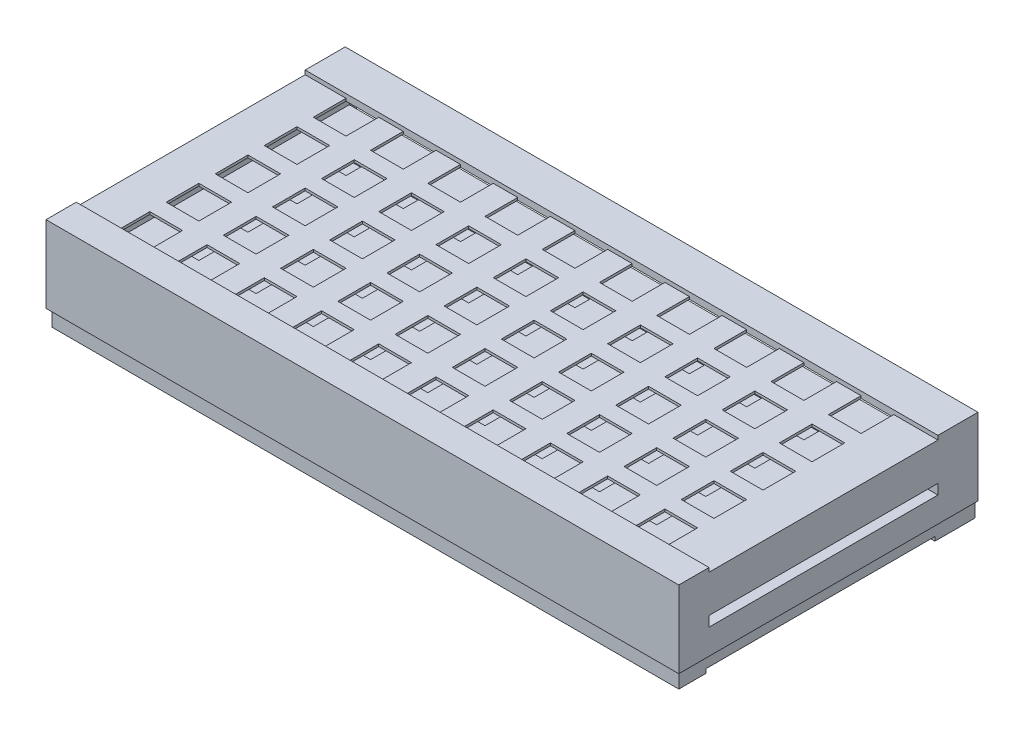
SolidWorks part; units mm, degrees
material "ABS"
ref_plane "Płaszczyzna przednia" through (0, 0, 0) normal (0, 0, 1) x (1, 0, 0)
ref_plane "Płaszczyzna górna" through (0, 0, 0) normal (0, 1, 0) x (1, 0, 0)
ref_plane "Płaszczyzna prawa" through (0, 0, 0) normal (1, 0, 0) x (0, 0, -1)
sketch "Szkic1" plane through (0, 0, 0) normal (0, 0, 1) x (1, 0, 0)
  line L15 (186, 34.1) -> (-188, 34.1)
  line L16 (186, 34.1) -> (186, -18.9)
  line L17 (186, -18.9) -> (-188, -18.9)
  line L18 (-188, 34.1) -> (-188, -18.9)
  point P0 (0, 0)
  dimension "D3" = 374
  dimension "D6" = 53
extrude "Dodanie-wyciągnięcie1" add sketch "Szkic1" along normal blind 177 contours L17 L18 L15 L16
sketch "Szkic5" plane through (0, -18.9, 0) normal (0, -1, 0) x (1, 0, 0)
  line L0 (186, 0) -> (-188, 0) construction
  line L1 (165.5, 48.5) -> (145.5, 48.5)
  line L2 (186, 177) -> (186, 0) construction
  line L3 (165.5, 48.5) -> (165.5, 68.5)
  line L4 (165.5, 68.5) -> (145.5, 68.5)
  line L5 (165.5, 18.5) -> (145.5, 18.5)
  line L6 (165.5, 18.5) -> (165.5, 38.5)
  line L7 (165.5, 38.5) -> (145.5, 38.5)
  line L8 (145.5, 18.5) -> (145.5, 38.5)
  line L9 (145.5, 48.5) -> (145.5, 68.5)
  line L10 (165.5, 78.5) -> (145.5, 78.5)
  line L11 (165.5, 78.5) -> (165.5, 98.5)
  line L12 (165.5, 98.5) -> (145.5, 98.5)
  line L13 (145.5, 78.5) -> (145.5, 98.5)
  line L14 (165.5, 108.5) -> (145.5, 108.5)
  line L15 (165.5, 108.5) -> (165.5, 128.5)
  line L16 (165.5, 128.5) -> (145.5, 128.5)
  line L17 (145.5, 108.5) -> (145.5, 128.5)
  line L18 (165.5, 138.5) -> (145.5, 138.5)
  line L19 (165.5, 138.5) -> (165.5, 158.5)
  line L20 (165.5, 158.5) -> (145.5, 158.5)
  line L21 (145.5, 138.5) -> (145.5, 158.5)
  line L22 (130.5, 48.5) -> (110.5, 48.5)
  line L23 (130.5, 48.5) -> (130.5, 68.5)
  line L24 (130.5, 68.5) -> (110.5, 68.5)
  line L25 (130.5, 18.5) -> (110.5, 18.5)
  line L26 (130.5, 18.5) -> (130.5, 38.5)
  line L27 (130.5, 38.5) -> (110.5, 38.5)
  line L28 (110.5, 18.5) -> (110.5, 38.5)
  line L29 (110.5, 48.5) -> (110.5, 68.5)
  line L30 (130.5, 78.5) -> (110.5, 78.5)
  line L31 (130.5, 78.5) -> (130.5, 98.5)
  line L32 (130.5, 98.5) -> (110.5, 98.5)
  line L33 (110.5, 78.5) -> (110.5, 98.5)
  line L34 (130.5, 108.5) -> (110.5, 108.5)
  line L35 (130.5, 108.5) -> (130.5, 128.5)
  line L36 (130.5, 128.5) -> (110.5, 128.5)
  line L37 (110.5, 108.5) -> (110.5, 128.5)
  line L38 (130.5, 138.5) -> (110.5, 138.5)
  line L39 (130.5, 138.5) -> (130.5, 158.5)
  line L40 (130.5, 158.5) -> (110.5, 158.5)
  line L41 (110.5, 138.5) -> (110.5, 158.5)
  line L42 (95.5, 48.5) -> (75.5, 48.5)
  line L43 (95.5, 48.5) -> (95.5, 68.5)
  line L44 (95.5, 68.5) -> (75.5, 68.5)
  line L45 (95.5, 18.5) -> (75.5, 18.5)
  line L46 (95.5, 18.5) -> (95.5, 38.5)
  line L47 (95.5, 38.5) -> (75.5, 38.5)
  line L48 (75.5, 18.5) -> (75.5, 38.5)
  line L49 (75.5, 48.5) -> (75.5, 68.5)
  line L50 (95.5, 78.5) -> (75.5, 78.5)
  line L51 (95.5, 78.5) -> (95.5, 98.5)
  line L52 (95.5, 98.5) -> (75.5, 98.5)
  line L53 (75.5, 78.5) -> (75.5, 98.5)
  line L54 (95.5, 108.5) -> (75.5, 108.5)
  line L55 (95.5, 108.5) -> (95.5, 128.5)
  line L56 (95.5, 128.5) -> (75.5, 128.5)
  line L57 (75.5, 108.5) -> (75.5, 128.5)
  line L58 (95.5, 138.5) -> (75.5, 138.5)
  line L59 (95.5, 138.5) -> (95.5, 158.5)
  line L60 (95.5, 158.5) -> (75.5, 158.5)
  line L61 (75.5, 138.5) -> (75.5, 158.5)
  line L62 (60.5, 48.5) -> (40.5, 48.5)
  line L63 (60.5, 48.5) -> (60.5, 68.5)
  line L64 (60.5, 68.5) -> (40.5, 68.5)
  line L65 (60.5, 18.5) -> (40.5, 18.5)
  line L66 (60.5, 18.5) -> (60.5, 38.5)
  line L67 (60.5, 38.5) -> (40.5, 38.5)
  line L68 (40.5, 18.5) -> (40.5, 38.5)
  line L69 (40.5, 48.5) -> (40.5, 68.5)
  line L70 (60.5, 78.5) -> (40.5, 78.5)
  line L71 (60.5, 78.5) -> (60.5, 98.5)
  line L72 (60.5, 98.5) -> (40.5, 98.5)
  line L73 (40.5, 78.5) -> (40.5, 98.5)
  line L74 (60.5, 108.5) -> (40.5, 108.5)
  line L75 (60.5, 108.5) -> (60.5, 128.5)
  line L76 (60.5, 128.5) -> (40.5, 128.5)
  line L77 (40.5, 108.5) -> (40.5, 128.5)
  line L78 (60.5, 138.5) -> (40.5, 138.5)
  line L79 (60.5, 138.5) -> (60.5, 158.5)
  line L80 (60.5, 158.5) -> (40.5, 158.5)
  line L81 (40.5, 138.5) -> (40.5, 158.5)
  line L82 (25.5, 48.5) -> (5.5, 48.5)
  line L83 (25.5, 48.5) -> (25.5, 68.5)
  line L84 (25.5, 68.5) -> (5.5, 68.5)
  line L85 (25.5, 18.5) -> (5.5, 18.5)
  line L86 (25.5, 18.5) -> (25.5, 38.5)
  line L87 (25.5, 38.5) -> (5.5, 38.5)
  line L88 (5.5, 18.5) -> (5.5, 38.5)
  line L89 (5.5, 48.5) -> (5.5, 68.5)
  line L90 (25.5, 78.5) -> (5.5, 78.5)
  line L91 (25.5, 78.5) -> (25.5, 98.5)
  line L92 (25.5, 98.5) -> (5.5, 98.5)
  line L93 (5.5, 78.5) -> (5.5, 98.5)
  line L94 (25.5, 108.5) -> (5.5, 108.5)
  line L95 (25.5, 108.5) -> (25.5, 128.5)
  line L96 (25.5, 128.5) -> (5.5, 128.5)
  line L97 (5.5, 108.5) -> (5.5, 128.5)
  line L98 (25.5, 138.5) -> (5.5, 138.5)
  line L99 (25.5, 138.5) -> (25.5, 158.5)
  line L100 (25.5, 158.5) -> (5.5, 158.5)
  line L101 (5.5, 138.5) -> (5.5, 158.5)
  line L102 (-9.5, 48.5) -> (-29.5, 48.5)
  line L103 (-9.5, 48.5) -> (-9.5, 68.5)
  line L104 (-9.5, 68.5) -> (-29.5, 68.5)
  line L105 (-9.5, 18.5) -> (-29.5, 18.5)
  line L106 (-9.5, 18.5) -> (-9.5, 38.5)
  line L107 (-9.5, 38.5) -> (-29.5, 38.5)
  line L108 (-29.5, 18.5) -> (-29.5, 38.5)
  line L109 (-29.5, 48.5) -> (-29.5, 68.5)
  line L110 (-9.5, 78.5) -> (-29.5, 78.5)
  line L111 (-9.5, 78.5) -> (-9.5, 98.5)
  line L112 (-9.5, 98.5) -> (-29.5, 98.5)
  line L113 (-29.5, 78.5) -> (-29.5, 98.5)
  line L114 (-9.5, 108.5) -> (-29.5, 108.5)
  line L115 (-9.5, 108.5) -> (-9.5, 128.5)
  line L116 (-9.5, 128.5) -> (-29.5, 128.5)
  line L117 (-29.5, 108.5) -> (-29.5, 128.5)
  line L118 (-9.5, 138.5) -> (-29.5, 138.5)
  line L119 (-9.5, 138.5) -> (-9.5, 158.5)
  line L120 (-9.5, 158.5) -> (-29.5, 158.5)
  line L121 (-29.5, 138.5) -> (-29.5, 158.5)
  line L122 (-44.5, 48.5) -> (-64.5, 48.5)
  line L123 (-44.5, 48.5) -> (-44.5, 68.5)
  line L124 (-44.5, 68.5) -> (-64.5, 68.5)
  line L125 (-44.5, 18.5) -> (-64.5, 18.5)
  line L126 (-44.5, 18.5) -> (-44.5, 38.5)
  line L127 (-44.5, 38.5) -> (-64.5, 38.5)
  line L128 (-64.5, 18.5) -> (-64.5, 38.5)
  line L129 (-64.5, 48.5) -> (-64.5, 68.5)
  line L130 (-44.5, 78.5) -> (-64.5, 78.5)
  line L131 (-44.5, 78.5) -> (-44.5, 98.5)
  line L132 (-44.5, 98.5) -> (-64.5, 98.5)
  line L133 (-64.5, 78.5) -> (-64.5, 98.5)
  line L134 (-44.5, 108.5) -> (-64.5, 108.5)
  line L135 (-44.5, 108.5) -> (-44.5, 128.5)
  line L136 (-44.5, 128.5) -> (-64.5, 128.5)
  line L137 (-64.5, 108.5) -> (-64.5, 128.5)
  line L138 (-44.5, 138.5) -> (-64.5, 138.5)
  line L139 (-44.5, 138.5) -> (-44.5, 158.5)
  line L140 (-44.5, 158.5) -> (-64.5, 158.5)
  line L141 (-64.5, 138.5) -> (-64.5, 158.5)
  line L142 (-79.5, 48.5) -> (-99.5, 48.5)
  line L143 (-79.5, 48.5) -> (-79.5, 68.5)
  line L144 (-79.5, 68.5) -> (-99.5, 68.5)
  line L145 (-79.5, 18.5) -> (-99.5, 18.5)
  line L146 (-79.5, 18.5) -> (-79.5, 38.5)
  line L147 (-79.5, 38.5) -> (-99.5, 38.5)
  line L148 (-99.5, 18.5) -> (-99.5, 38.5)
  line L149 (-99.5, 48.5) -> (-99.5, 68.5)
  line L150 (-79.5, 78.5) -> (-99.5, 78.5)
  line L151 (-79.5, 78.5) -> (-79.5, 98.5)
  line L152 (-79.5, 98.5) -> (-99.5, 98.5)
  line L153 (-99.5, 78.5) -> (-99.5, 98.5)
  line L154 (-79.5, 108.5) -> (-99.5, 108.5)
  line L155 (-79.5, 108.5) -> (-79.5, 128.5)
  line L156 (-79.5, 128.5) -> (-99.5, 128.5)
  line L157 (-99.5, 108.5) -> (-99.5, 128.5)
  line L158 (-79.5, 138.5) -> (-99.5, 138.5)
  line L159 (-79.5, 138.5) -> (-79.5, 158.5)
  line L160 (-79.5, 158.5) -> (-99.5, 158.5)
  line L161 (-99.5, 138.5) -> (-99.5, 158.5)
  line L162 (-114.5, 48.5) -> (-134.5, 48.5)
  line L163 (-114.5, 48.5) -> (-114.5, 68.5)
  line L164 (-114.5, 68.5) -> (-134.5, 68.5)
  line L165 (-114.5, 18.5) -> (-134.5, 18.5)
  line L166 (-114.5, 18.5) -> (-114.5, 38.5)
  line L167 (-114.5, 38.5) -> (-134.5, 38.5)
  line L168 (-134.5, 18.5) -> (-134.5, 38.5)
  line L169 (-134.5, 48.5) -> (-134.5, 68.5)
  line L170 (-114.5, 78.5) -> (-134.5, 78.5)
  line L171 (-114.5, 78.5) -> (-114.5, 98.5)
  line L172 (-114.5, 98.5) -> (-134.5, 98.5)
  line L173 (-134.5, 78.5) -> (-134.5, 98.5)
  line L174 (-114.5, 108.5) -> (-134.5, 108.5)
  line L175 (-114.5, 108.5) -> (-114.5, 128.5)
  line L176 (-114.5, 128.5) -> (-134.5, 128.5)
  line L177 (-134.5, 108.5) -> (-134.5, 128.5)
  line L178 (-114.5, 138.5) -> (-134.5, 138.5)
  line L179 (-114.5, 138.5) -> (-114.5, 158.5)
  line L180 (-114.5, 158.5) -> (-134.5, 158.5)
  line L181 (-134.5, 138.5) -> (-134.5, 158.5)
  line L182 (-149.5, 48.5) -> (-169.5, 48.5)
  line L183 (-149.5, 48.5) -> (-149.5, 68.5)
  line L184 (-149.5, 68.5) -> (-169.5, 68.5)
  line L185 (-149.5, 18.5) -> (-169.5, 18.5)
  line L186 (-149.5, 18.5) -> (-149.5, 38.5)
  line L187 (-149.5, 38.5) -> (-169.5, 38.5)
  line L188 (-169.5, 18.5) -> (-169.5, 38.5)
  line L189 (-169.5, 48.5) -> (-169.5, 68.5)
  line L190 (-149.5, 78.5) -> (-169.5, 78.5)
  line L191 (-149.5, 78.5) -> (-149.5, 98.5)
  line L192 (-149.5, 98.5) -> (-169.5, 98.5)
  line L193 (-169.5, 78.5) -> (-169.5, 98.5)
  line L194 (-149.5, 108.5) -> (-169.5, 108.5)
  line L195 (-149.5, 108.5) -> (-149.5, 128.5)
  line L196 (-149.5, 128.5) -> (-169.5, 128.5)
  line L197 (-169.5, 108.5) -> (-169.5, 128.5)
  line L198 (-149.5, 138.5) -> (-169.5, 138.5)
  line L199 (-149.5, 138.5) -> (-149.5, 158.5)
  line L200 (-149.5, 158.5) -> (-169.5, 158.5)
  line L201 (-169.5, 138.5) -> (-169.5, 158.5)
  line L202 (186, 177) -> (-188, 177) construction
  line L203 (-188, 177) -> (-188, 0) construction
  dimension "D1" = 18.5
  dimension "D2" = 20.5
  dimension "D3" = 20
  dimension "D4" = 20
  dimension "D7" = 20
  dimension "D8" = 20
  dimension "D9" = 15
  dimension "D10" = 18.5
  dimension "D11" = 18.5
  dimension "D5" = 5
  dimension "D6" = 10
extrude "Wytnij-wyciągnięcie4" cut sketch "Szkic5" against normal blind 104
sketch "Szkic7" plane through (0, 0, 0) normal (0, 0, -1) x (-1, 0, 0)
  line L5 (-186, -18.9) -> (188, -18.9) construction
  line L7 (-184, 32.1) -> (186, 32.1)
  line L8 (-184, 32.1) -> (-184, 12.7)
  line L9 (-184, 12.7) -> (186, 12.7)
  line L10 (186, 32.1) -> (186, 12.7)
  line L12 (-186, 34.1) -> (-186, -18.9) construction
  line L13 (-184, -16.9) -> (186, -16.9)
  line L14 (-184, -16.9) -> (-184, 2.5)
  line L15 (-184, 2.5) -> (186, 2.5)
  line L16 (186, -16.9) -> (186, 2.5)
  line L17 (-186, 34.1) -> (188, 34.1) construction
  dimension "D1" = 370
  dimension "D2" = 2
  dimension "D3" = 2
  dimension "D4" = 2
  dimension "D5" = 2
  dimension "D6" = 370
  dimension "D7" = 370
  dimension "D8" = 19.4
  dimension "D9" = 19.4
extrude "Wytnij-wyciągnięcie5" cut sketch "Szkic7" against normal blind 175
sketch "Szkic9" plane through (186, 0, 0) normal (1, 0, 0) x (0, 0, -1)
  line L15 (-158.5, 10.7) -> (-158.5, 4.5)
  line L17 (-18.5, 10.7) -> (-158.5, 10.7)
  line L18 (-18.5, 10.7) -> (-18.5, 4.5)
  line L19 (-18.5, 4.5) -> (-158.5, 4.5)
extrude "Wytnij-wyciągnięcie6" cut sketch "Szkic9" against normal blind 374
sketch "Szkic15" plane through (0, 34.1, 0) normal (0, 1, 0) x (1, 0, 0)
  line L1 (-188, 0) -> (186, 0)
  line L2 (-188, 0) -> (-188, -177)
  line L3 (-188, -177) -> (186, -177)
  line L4 (186, 0) -> (186, -177)
  line L5 (-169.5, -18.5) -> (-149.5, -18.5)
  line L6 (-169.5, -18.5) -> (-169.5, -38.5)
  line L7 (-169.5, -38.5) -> (-149.5, -38.5)
  line L8 (-149.5, -18.5) -> (-149.5, -38.5)
  line L9 (-134.5, -18.5) -> (-114.5, -18.5)
  line L10 (-134.5, -18.5) -> (-134.5, -38.5)
  line L11 (-134.5, -38.5) -> (-114.5, -38.5)
  line L12 (-114.5, -18.5) -> (-114.5, -38.5)
  line L13 (-99.5, -18.5) -> (-79.5, -18.5)
  line L14 (-99.5, -18.5) -> (-99.5, -38.5)
  line L15 (-99.5, -38.5) -> (-79.5, -38.5)
  line L16 (-79.5, -18.5) -> (-79.5, -38.5)
  line L17 (-64.5, -18.5) -> (-44.5, -18.5)
  line L18 (-64.5, -18.5) -> (-64.5, -38.5)
  line L19 (-64.5, -38.5) -> (-44.5, -38.5)
  line L20 (-44.5, -18.5) -> (-44.5, -38.5)
  line L21 (-29.5, -18.5) -> (-9.5, -18.5)
  line L22 (-29.5, -18.5) -> (-29.5, -38.5)
  line L23 (-29.5, -38.5) -> (-9.5, -38.5)
  line L24 (-9.5, -18.5) -> (-9.5, -38.5)
  line L25 (5.5, -18.5) -> (25.5, -18.5)
  line L26 (5.5, -18.5) -> (5.5, -38.5)
  line L27 (5.5, -38.5) -> (25.5, -38.5)
  line L28 (25.5, -18.5) -> (25.5, -38.5)
  line L29 (40.5, -18.5) -> (60.5, -18.5)
  line L30 (40.5, -18.5) -> (40.5, -38.5)
  line L31 (40.5, -38.5) -> (60.5, -38.5)
  line L32 (60.5, -18.5) -> (60.5, -38.5)
  line L33 (75.5, -18.5) -> (95.5, -18.5)
  line L34 (75.5, -18.5) -> (75.5, -38.5)
  line L35 (75.5, -38.5) -> (95.5, -38.5)
  line L36 (95.5, -18.5) -> (95.5, -38.5)
  line L37 (110.5, -18.5) -> (130.5, -18.5)
  line L38 (110.5, -18.5) -> (110.5, -38.5)
  line L39 (110.5, -38.5) -> (130.5, -38.5)
  line L40 (130.5, -18.5) -> (130.5, -38.5)
  line L41 (145.5, -18.5) -> (165.5, -18.5)
  line L42 (145.5, -18.5) -> (145.5, -38.5)
  line L43 (145.5, -38.5) -> (165.5, -38.5)
  line L44 (165.5, -18.5) -> (165.5, -38.5)
  line L45 (145.5, -48.5) -> (165.5, -48.5)
  line L46 (145.5, -48.5) -> (145.5, -68.5)
  line L47 (145.5, -68.5) -> (165.5, -68.5)
  line L48 (165.5, -48.5) -> (165.5, -68.5)
  line L49 (145.5, -78.5) -> (165.5, -78.5)
  line L50 (145.5, -78.5) -> (145.5, -98.5)
  line L51 (145.5, -98.5) -> (165.5, -98.5)
  line L52 (165.5, -78.5) -> (165.5, -98.5)
  line L53 (145.5, -108.5) -> (165.5, -108.5)
  line L54 (145.5, -108.5) -> (145.5, -128.5)
  line L55 (145.5, -128.5) -> (165.5, -128.5)
  line L56 (165.5, -108.5) -> (165.5, -128.5)
  line L57 (145.5, -138.5) -> (165.5, -138.5)
  line L58 (145.5, -138.5) -> (145.5, -158.5)
  line L59 (145.5, -158.5) -> (165.5, -158.5)
  line L60 (165.5, -138.5) -> (165.5, -158.5)
  line L61 (110.5, -48.5) -> (130.5, -48.5)
  line L62 (110.5, -48.5) -> (110.5, -68.5)
  line L63 (110.5, -68.5) -> (130.5, -68.5)
  line L64 (130.5, -48.5) -> (130.5, -68.5)
  line L65 (110.5, -78.5) -> (130.5, -78.5)
  line L66 (110.5, -78.5) -> (110.5, -98.5)
  line L67 (110.5, -98.5) -> (130.5, -98.5)
  line L68 (130.5, -78.5) -> (130.5, -98.5)
  line L69 (110.5, -108.5) -> (130.5, -108.5)
  line L70 (110.5, -108.5) -> (110.5, -128.5)
  line L71 (110.5, -128.5) -> (130.5, -128.5)
  line L72 (130.5, -108.5) -> (130.5, -128.5)
  line L73 (110.5, -138.5) -> (130.5, -138.5)
  line L74 (110.5, -138.5) -> (110.5, -158.5)
  line L75 (110.5, -158.5) -> (130.5, -158.5)
  line L76 (130.5, -138.5) -> (130.5, -158.5)
  line L77 (75.5, -48.5) -> (95.5, -48.5)
  line L78 (75.5, -48.5) -> (75.5, -68.5)
  line L79 (75.5, -68.5) -> (95.5, -68.5)
  line L80 (95.5, -48.5) -> (95.5, -68.5)
  line L81 (75.5, -78.5) -> (95.5, -78.5)
  line L82 (75.5, -78.5) -> (75.5, -98.5)
  line L83 (75.5, -98.5) -> (95.5, -98.5)
  line L84 (95.5, -78.5) -> (95.5, -98.5)
  line L85 (75.5, -108.5) -> (95.5, -108.5)
  line L86 (75.5, -108.5) -> (75.5, -128.5)
  line L87 (75.5, -128.5) -> (95.5, -128.5)
  line L88 (95.5, -108.5) -> (95.5, -128.5)
  line L89 (75.5, -138.5) -> (95.5, -138.5)
  line L90 (75.5, -138.5) -> (75.5, -158.5)
  line L91 (75.5, -158.5) -> (95.5, -158.5)
  line L92 (95.5, -138.5) -> (95.5, -158.5)
  line L93 (40.5, -48.5) -> (60.5, -48.5)
  line L94 (40.5, -48.5) -> (40.5, -68.5)
  line L95 (40.5, -68.5) -> (60.5, -68.5)
  line L96 (60.5, -48.5) -> (60.5, -68.5)
  line L97 (40.5, -78.5) -> (60.5, -78.5)
  line L98 (40.5, -78.5) -> (40.5, -98.5)
  line L99 (40.5, -98.5) -> (60.5, -98.5)
  line L100 (60.5, -78.5) -> (60.5, -98.5)
  line L101 (40.5, -108.5) -> (60.5, -108.5)
  line L102 (40.5, -108.5) -> (40.5, -128.5)
  line L103 (40.5, -128.5) -> (60.5, -128.5)
  line L104 (60.5, -108.5) -> (60.5, -128.5)
  line L105 (5.5, -48.5) -> (25.5, -48.5)
  line L106 (5.5, -48.5) -> (5.5, -68.5)
  line L107 (5.5, -68.5) -> (25.5, -68.5)
  line L108 (25.5, -48.5) -> (25.5, -68.5)
  line L109 (5.5, -78.5) -> (25.5, -78.5)
  line L110 (5.5, -78.5) -> (5.5, -98.5)
  line L111 (5.5, -98.5) -> (25.5, -98.5)
  line L112 (25.5, -78.5) -> (25.5, -98.5)
  line L113 (5.5, -108.5) -> (25.5, -108.5)
  line L114 (5.5, -108.5) -> (5.5, -128.5)
  line L115 (5.5, -128.5) -> (25.5, -128.5)
  line L116 (25.5, -108.5) -> (25.5, -128.5)
  line L117 (5.5, -138.5) -> (25.5, -138.5)
  line L118 (5.5, -138.5) -> (5.5, -158.5)
  line L119 (5.5, -158.5) -> (25.5, -158.5)
  line L120 (25.5, -138.5) -> (25.5, -158.5)
  line L121 (40.5, -138.5) -> (60.5, -138.5)
  line L122 (40.5, -138.5) -> (40.5, -158.5)
  line L123 (40.5, -158.5) -> (60.5, -158.5)
  line L124 (60.5, -138.5) -> (60.5, -158.5)
  line L125 (-29.5, -48.5) -> (-9.5, -48.5)
  line L126 (-29.5, -48.5) -> (-29.5, -68.5)
  line L127 (-29.5, -68.5) -> (-9.5, -68.5)
  line L128 (-9.5, -48.5) -> (-9.5, -68.5)
  line L129 (-29.5, -78.5) -> (-9.5, -78.5)
  line L130 (-29.5, -78.5) -> (-29.5, -98.5)
  line L131 (-29.5, -98.5) -> (-9.5, -98.5)
  line L132 (-9.5, -78.5) -> (-9.5, -98.5)
  line L133 (-29.5, -108.5) -> (-9.5, -108.5)
  line L134 (-29.5, -108.5) -> (-29.5, -128.5)
  line L135 (-29.5, -128.5) -> (-9.5, -128.5)
  line L136 (-9.5, -108.5) -> (-9.5, -128.5)
  line L137 (-29.5, -138.5) -> (-9.5, -138.5)
  line L138 (-29.5, -138.5) -> (-29.5, -158.5)
  line L139 (-29.5, -158.5) -> (-9.5, -158.5)
  line L140 (-9.5, -138.5) -> (-9.5, -158.5)
  line L141 (-64.5, -48.5) -> (-44.5, -48.5)
  line L142 (-64.5, -48.5) -> (-64.5, -68.5)
  line L143 (-64.5, -68.5) -> (-44.5, -68.5)
  line L144 (-44.5, -48.5) -> (-44.5, -68.5)
  line L145 (-64.5, -78.5) -> (-44.5, -78.5)
  line L146 (-64.5, -78.5) -> (-64.5, -98.5)
  line L147 (-64.5, -98.5) -> (-44.5, -98.5)
  line L148 (-44.5, -78.5) -> (-44.5, -98.5)
  line L149 (-64.5, -108.5) -> (-44.5, -108.5)
  line L150 (-64.5, -108.5) -> (-64.5, -128.5)
  line L151 (-64.5, -128.5) -> (-44.5, -128.5)
  line L152 (-44.5, -108.5) -> (-44.5, -128.5)
  line L153 (-64.5, -138.5) -> (-44.5, -138.5)
  line L154 (-64.5, -138.5) -> (-64.5, -158.5)
  line L155 (-64.5, -158.5) -> (-44.5, -158.5)
  line L156 (-44.5, -138.5) -> (-44.5, -158.5)
  line L157 (-99.5, -48.5) -> (-79.5, -48.5)
  line L158 (-99.5, -48.5) -> (-99.5, -68.5)
  line L159 (-99.5, -68.5) -> (-79.5, -68.5)
  line L160 (-79.5, -48.5) -> (-79.5, -68.5)
  line L161 (-99.5, -78.5) -> (-79.5, -78.5)
  line L162 (-99.5, -78.5) -> (-99.5, -98.5)
  line L163 (-99.5, -98.5) -> (-79.5, -98.5)
  line L164 (-79.5, -78.5) -> (-79.5, -98.5)
  line L165 (-99.5, -108.5) -> (-79.5, -108.5)
  line L166 (-99.5, -108.5) -> (-99.5, -128.5)
  line L167 (-99.5, -128.5) -> (-79.5, -128.5)
  line L168 (-79.5, -108.5) -> (-79.5, -128.5)
  line L169 (-99.5, -138.5) -> (-79.5, -138.5)
  line L170 (-99.5, -138.5) -> (-99.5, -158.5)
  line L171 (-99.5, -158.5) -> (-79.5, -158.5)
  line L172 (-79.5, -138.5) -> (-79.5, -158.5)
  line L173 (-134.5, -48.5) -> (-114.5, -48.5)
  line L174 (-134.5, -48.5) -> (-134.5, -68.5)
  line L175 (-134.5, -68.5) -> (-114.5, -68.5)
  line L176 (-114.5, -48.5) -> (-114.5, -68.5)
  line L177 (-134.5, -78.5) -> (-114.5, -78.5)
  line L178 (-134.5, -78.5) -> (-134.5, -98.5)
  line L179 (-134.5, -98.5) -> (-114.5, -98.5)
  line L180 (-114.5, -78.5) -> (-114.5, -98.5)
  line L181 (-134.5, -108.5) -> (-114.5, -108.5)
  line L182 (-134.5, -108.5) -> (-134.5, -128.5)
  line L183 (-134.5, -128.5) -> (-114.5, -128.5)
  line L184 (-114.5, -108.5) -> (-114.5, -128.5)
  line L185 (-134.5, -138.5) -> (-114.5, -138.5)
  line L186 (-134.5, -138.5) -> (-134.5, -158.5)
  line L187 (-134.5, -158.5) -> (-114.5, -158.5)
  line L188 (-114.5, -138.5) -> (-114.5, -158.5)
  line L189 (-169.5, -48.5) -> (-149.5, -48.5)
  line L190 (-169.5, -48.5) -> (-169.5, -68.5)
  line L191 (-169.5, -68.5) -> (-149.5, -68.5)
  line L192 (-149.5, -48.5) -> (-149.5, -68.5)
  line L193 (-169.5, -78.5) -> (-149.5, -78.5)
  line L194 (-169.5, -78.5) -> (-169.5, -98.5)
  line L195 (-169.5, -98.5) -> (-149.5, -98.5)
  line L196 (-149.5, -78.5) -> (-149.5, -98.5)
  line L197 (-169.5, -108.5) -> (-149.5, -108.5)
  line L198 (-169.5, -108.5) -> (-169.5, -128.5)
  line L199 (-169.5, -128.5) -> (-149.5, -128.5)
  line L200 (-149.5, -108.5) -> (-149.5, -128.5)
  line L201 (-169.5, -138.5) -> (-149.5, -138.5)
  line L202 (-169.5, -138.5) -> (-169.5, -158.5)
  line L203 (-169.5, -158.5) -> (-149.5, -158.5)
  line L204 (-149.5, -138.5) -> (-149.5, -158.5)
extrude "Dodanie-wyciągnięcie6" add sketch "Szkic15" along normal blind 1
sketch "Szkic16" plane through (0, -18.9, 0) normal (0, -1, 0) x (1, 0, 0)
  line L1 (186, 0) -> (-188, 0)
  line L2 (186, 0) -> (186, 177)
  line L3 (186, 177) -> (-188, 177)
  line L4 (-188, 0) -> (-188, 177)
  line L5 (165.5, 18.5) -> (145.5, 18.5)
  line L6 (165.5, 18.5) -> (165.5, 38.5)
  line L7 (165.5, 38.5) -> (145.5, 38.5)
  line L8 (145.5, 18.5) -> (145.5, 38.5)
  line L9 (130.5, 18.5) -> (110.5, 18.5)
  line L10 (130.5, 18.5) -> (130.5, 38.5)
  line L11 (130.5, 38.5) -> (110.5, 38.5)
  line L12 (110.5, 18.5) -> (110.5, 38.5)
  line L13 (95.5, 18.5) -> (75.5, 18.5)
  line L14 (95.5, 18.5) -> (95.5, 38.5)
  line L15 (95.5, 38.5) -> (75.5, 38.5)
  line L16 (75.5, 18.5) -> (75.5, 38.5)
  line L17 (60.5, 18.5) -> (40.5, 18.5)
  line L18 (60.5, 18.5) -> (60.5, 38.5)
  line L19 (60.5, 38.5) -> (40.5, 38.5)
  line L20 (40.5, 18.5) -> (40.5, 38.5)
  line L21 (25.5, 18.5) -> (5.5, 18.5)
  line L22 (25.5, 18.5) -> (25.5, 38.5)
  line L23 (25.5, 38.5) -> (5.5, 38.5)
  line L24 (5.5, 18.5) -> (5.5, 38.5)
  line L25 (-9.5, 18.5) -> (-29.5, 18.5)
  line L26 (-9.5, 18.5) -> (-9.5, 38.5)
  line L27 (-9.5, 38.5) -> (-29.5, 38.5)
  line L28 (-29.5, 18.5) -> (-29.5, 38.5)
  line L29 (-44.5, 18.5) -> (-64.5, 18.5)
  line L30 (-44.5, 18.5) -> (-44.5, 38.5)
  line L31 (-44.5, 38.5) -> (-64.5, 38.5)
  line L32 (-64.5, 18.5) -> (-64.5, 38.5)
  line L33 (-79.5, 18.5) -> (-99.5, 18.5)
  line L34 (-79.5, 18.5) -> (-79.5, 38.5)
  line L35 (-79.5, 38.5) -> (-99.5, 38.5)
  line L36 (-99.5, 18.5) -> (-99.5, 38.5)
  line L37 (-114.5, 18.5) -> (-134.5, 18.5)
  line L38 (-114.5, 18.5) -> (-114.5, 38.5)
  line L39 (-114.5, 38.5) -> (-134.5, 38.5)
  line L40 (-134.5, 18.5) -> (-134.5, 38.5)
  line L41 (-149.5, 18.5) -> (-169.5, 18.5)
  line L42 (-149.5, 18.5) -> (-149.5, 38.5)
  line L43 (-149.5, 38.5) -> (-169.5, 38.5)
  line L44 (-169.5, 18.5) -> (-169.5, 38.5)
  line L45 (165.5, 48.5) -> (145.5, 48.5)
  line L46 (165.5, 48.5) -> (165.5, 68.5)
  line L47 (165.5, 68.5) -> (145.5, 68.5)
  line L48 (145.5, 48.5) -> (145.5, 68.5)
  line L49 (130.5, 48.5) -> (110.5, 48.5)
  line L50 (130.5, 48.5) -> (130.5, 68.5)
  line L51 (130.5, 68.5) -> (110.5, 68.5)
  line L52 (110.5, 48.5) -> (110.5, 68.5)
  line L53 (95.5, 48.5) -> (75.5, 48.5)
  line L54 (95.5, 48.5) -> (95.5, 68.5)
  line L55 (95.5, 68.5) -> (75.5, 68.5)
  line L56 (75.5, 48.5) -> (75.5, 68.5)
  line L57 (60.5, 48.5) -> (40.5, 48.5)
  line L58 (60.5, 48.5) -> (60.5, 68.5)
  line L59 (60.5, 68.5) -> (40.5, 68.5)
  line L60 (40.5, 48.5) -> (40.5, 68.5)
  line L61 (25.5, 48.5) -> (5.5, 48.5)
  line L62 (25.5, 48.5) -> (25.5, 68.5)
  line L63 (25.5, 68.5) -> (5.5, 68.5)
  line L64 (5.5, 48.5) -> (5.5, 68.5)
  line L65 (-9.5, 48.5) -> (-29.5, 48.5)
  line L66 (-9.5, 48.5) -> (-9.5, 68.5)
  line L67 (-9.5, 68.5) -> (-29.5, 68.5)
  line L68 (-29.5, 48.5) -> (-29.5, 68.5)
  line L69 (-44.5, 48.5) -> (-64.5, 48.5)
  line L70 (-44.5, 48.5) -> (-44.5, 68.5)
  line L71 (-44.5, 68.5) -> (-64.5, 68.5)
  line L72 (-64.5, 48.5) -> (-64.5, 68.5)
  line L73 (-79.5, 48.5) -> (-99.5, 48.5)
  line L74 (-79.5, 48.5) -> (-79.5, 68.5)
  line L75 (-79.5, 68.5) -> (-99.5, 68.5)
  line L76 (-99.5, 48.5) -> (-99.5, 68.5)
  line L77 (-114.5, 48.5) -> (-134.5, 48.5)
  line L78 (-114.5, 48.5) -> (-114.5, 68.5)
  line L79 (-114.5, 68.5) -> (-134.5, 68.5)
  line L80 (-134.5, 48.5) -> (-134.5, 68.5)
  line L81 (-149.5, 48.5) -> (-169.5, 48.5)
  line L82 (-149.5, 48.5) -> (-149.5, 68.5)
  line L83 (-149.5, 68.5) -> (-169.5, 68.5)
  line L84 (-169.5, 48.5) -> (-169.5, 68.5)
  line L85 (-149.5, 78.5) -> (-169.5, 78.5)
  line L86 (-149.5, 78.5) -> (-149.5, 98.5)
  line L87 (-149.5, 98.5) -> (-169.5, 98.5)
  line L88 (-169.5, 78.5) -> (-169.5, 98.5)
  line L89 (-149.5, 108.5) -> (-169.5, 108.5)
  line L90 (-149.5, 108.5) -> (-149.5, 128.5)
  line L91 (-149.5, 128.5) -> (-169.5, 128.5)
  line L92 (-169.5, 108.5) -> (-169.5, 128.5)
  line L93 (-149.5, 138.5) -> (-169.5, 138.5)
  line L94 (-149.5, 138.5) -> (-149.5, 158.5)
  line L95 (-149.5, 158.5) -> (-169.5, 158.5)
  line L96 (-169.5, 138.5) -> (-169.5, 158.5)
  line L97 (-114.5, 78.5) -> (-134.5, 78.5)
  line L98 (-114.5, 78.5) -> (-114.5, 98.5)
  line L99 (-114.5, 98.5) -> (-134.5, 98.5)
  line L100 (-134.5, 78.5) -> (-134.5, 98.5)
  line L101 (-114.5, 108.5) -> (-134.5, 108.5)
  line L102 (-114.5, 108.5) -> (-114.5, 128.5)
  line L103 (-114.5, 128.5) -> (-134.5, 128.5)
  line L104 (-134.5, 108.5) -> (-134.5, 128.5)
  line L105 (-114.5, 138.5) -> (-134.5, 138.5)
  line L106 (-114.5, 138.5) -> (-114.5, 158.5)
  line L107 (-114.5, 158.5) -> (-134.5, 158.5)
  line L108 (-134.5, 138.5) -> (-134.5, 158.5)
  line L109 (-79.5, 78.5) -> (-99.5, 78.5)
  line L110 (-79.5, 78.5) -> (-79.5, 98.5)
  line L111 (-79.5, 98.5) -> (-99.5, 98.5)
  line L112 (-99.5, 78.5) -> (-99.5, 98.5)
  line L113 (-79.5, 108.5) -> (-99.5, 108.5)
  line L114 (-79.5, 108.5) -> (-79.5, 128.5)
  line L115 (-79.5, 128.5) -> (-99.5, 128.5)
  line L116 (-99.5, 108.5) -> (-99.5, 128.5)
  line L117 (-79.5, 138.5) -> (-99.5, 138.5)
  line L118 (-79.5, 138.5) -> (-79.5, 158.5)
  line L119 (-79.5, 158.5) -> (-99.5, 158.5)
  line L120 (-99.5, 138.5) -> (-99.5, 158.5)
  line L121 (-44.5, 78.5) -> (-64.5, 78.5)
  line L122 (-44.5, 78.5) -> (-44.5, 98.5)
  line L123 (-44.5, 98.5) -> (-64.5, 98.5)
  line L124 (-64.5, 78.5) -> (-64.5, 98.5)
  line L125 (-44.5, 108.5) -> (-64.5, 108.5)
  line L126 (-44.5, 108.5) -> (-44.5, 128.5)
  line L127 (-44.5, 128.5) -> (-64.5, 128.5)
  line L128 (-64.5, 108.5) -> (-64.5, 128.5)
  line L129 (-44.5, 138.5) -> (-64.5, 138.5)
  line L130 (-44.5, 138.5) -> (-44.5, 158.5)
  line L131 (-44.5, 158.5) -> (-64.5, 158.5)
  line L132 (-64.5, 138.5) -> (-64.5, 158.5)
  line L133 (-9.5, 78.5) -> (-29.5, 78.5)
  line L134 (-9.5, 78.5) -> (-9.5, 98.5)
  line L135 (-9.5, 98.5) -> (-29.5, 98.5)
  line L136 (-29.5, 78.5) -> (-29.5, 98.5)
  line L137 (-9.5, 108.5) -> (-29.5, 108.5)
  line L138 (-9.5, 108.5) -> (-9.5, 128.5)
  line L139 (-9.5, 128.5) -> (-29.5, 128.5)
  line L140 (-29.5, 108.5) -> (-29.5, 128.5)
  line L141 (-9.5, 138.5) -> (-29.5, 138.5)
  line L142 (-9.5, 138.5) -> (-9.5, 158.5)
  line L143 (-9.5, 158.5) -> (-29.5, 158.5)
  line L144 (-29.5, 138.5) -> (-29.5, 158.5)
  line L145 (25.5, 78.5) -> (5.5, 78.5)
  line L146 (25.5, 78.5) -> (25.5, 98.5)
  line L147 (25.5, 98.5) -> (5.5, 98.5)
  line L148 (5.5, 78.5) -> (5.5, 98.5)
  line L149 (25.5, 108.5) -> (5.5, 108.5)
  line L150 (25.5, 108.5) -> (25.5, 128.5)
  line L151 (25.5, 128.5) -> (5.5, 128.5)
  line L152 (5.5, 108.5) -> (5.5, 128.5)
  line L153 (25.5, 138.5) -> (5.5, 138.5)
  line L154 (25.5, 138.5) -> (25.5, 158.5)
  line L155 (25.5, 158.5) -> (5.5, 158.5)
  line L156 (5.5, 138.5) -> (5.5, 158.5)
  line L157 (60.5, 78.5) -> (40.5, 78.5)
  line L158 (60.5, 78.5) -> (60.5, 98.5)
  line L159 (60.5, 98.5) -> (40.5, 98.5)
  line L160 (40.5, 78.5) -> (40.5, 98.5)
  line L161 (60.5, 108.5) -> (40.5, 108.5)
  line L162 (60.5, 108.5) -> (60.5, 128.5)
  line L163 (60.5, 128.5) -> (40.5, 128.5)
  line L164 (40.5, 108.5) -> (40.5, 128.5)
  line L165 (60.5, 138.5) -> (40.5, 138.5)
  line L166 (60.5, 138.5) -> (60.5, 158.5)
  line L167 (60.5, 158.5) -> (40.5, 158.5)
  line L168 (40.5, 138.5) -> (40.5, 158.5)
  line L169 (95.5, 78.5) -> (75.5, 78.5)
  line L170 (95.5, 78.5) -> (95.5, 98.5)
  line L171 (95.5, 98.5) -> (75.5, 98.5)
  line L172 (75.5, 78.5) -> (75.5, 98.5)
  line L173 (95.5, 108.5) -> (75.5, 108.5)
  line L174 (95.5, 108.5) -> (95.5, 128.5)
  line L175 (95.5, 128.5) -> (75.5, 128.5)
  line L176 (75.5, 108.5) -> (75.5, 128.5)
  line L177 (95.5, 138.5) -> (75.5, 138.5)
  line L178 (95.5, 138.5) -> (95.5, 158.5)
  line L179 (95.5, 158.5) -> (75.5, 158.5)
  line L180 (75.5, 138.5) -> (75.5, 158.5)
  line L181 (130.5, 78.5) -> (110.5, 78.5)
  line L182 (130.5, 78.5) -> (130.5, 98.5)
  line L183 (130.5, 98.5) -> (110.5, 98.5)
  line L184 (110.5, 78.5) -> (110.5, 98.5)
  line L185 (165.5, 78.5) -> (145.5, 78.5)
  line L186 (165.5, 78.5) -> (165.5, 98.5)
  line L187 (165.5, 98.5) -> (145.5, 98.5)
  line L188 (145.5, 78.5) -> (145.5, 98.5)
  line L189 (165.5, 108.5) -> (145.5, 108.5)
  line L190 (165.5, 108.5) -> (165.5, 128.5)
  line L191 (165.5, 128.5) -> (145.5, 128.5)
  line L192 (145.5, 108.5) -> (145.5, 128.5)
  line L193 (130.5, 108.5) -> (110.5, 108.5)
  line L194 (130.5, 108.5) -> (130.5, 128.5)
  line L195 (130.5, 128.5) -> (110.5, 128.5)
  line L196 (110.5, 108.5) -> (110.5, 128.5)
  line L197 (165.5, 138.5) -> (145.5, 138.5)
  line L198 (165.5, 138.5) -> (165.5, 158.5)
  line L199 (165.5, 158.5) -> (145.5, 158.5)
  line L200 (145.5, 138.5) -> (145.5, 158.5)
  line L201 (130.5, 138.5) -> (110.5, 138.5)
  line L202 (130.5, 138.5) -> (130.5, 158.5)
  line L203 (130.5, 158.5) -> (110.5, 158.5)
  line L204 (110.5, 138.5) -> (110.5, 158.5)
extrude "Dodanie-wyciągnięcie7" add sketch "Szkic16" along normal blind 1
sketch "Szkic17" plane through (186, 0, 0) normal (1, 0, 0) x (0, 0, -1)
  line L1 (0, 35.1) -> (-177, 35.1)
  line L2 (0, 35.1) -> (0, -19.9)
  line L3 (0, -19.9) -> (-177, -19.9)
  line L4 (-177, 35.1) -> (-177, -19.9)
  line L5 (-18.5, 10.7) -> (-158.5, 10.7)
  line L6 (-18.5, 10.7) -> (-18.5, 4.5)
  line L7 (-18.5, 4.5) -> (-158.5, 4.5)
  line L8 (-158.5, 10.7) -> (-158.5, 4.5)
extrude "Dodanie-wyciągnięcie8" add sketch "Szkic17" along normal blind 1
sketch "Szkic18" plane through (-188, 0, 0) normal (-1, 0, 0) x (0, 0, 1)
  line L1 (0, -19.9) -> (177, -19.9)
  line L2 (0, -19.9) -> (0, 35.1)
  line L3 (0, 35.1) -> (177, 35.1)
  line L4 (177, -19.9) -> (177, 35.1)
  line L5 (18.5, 4.5) -> (158.5, 4.5)
  line L6 (18.5, 4.5) -> (18.5, 10.7)
  line L7 (18.5, 10.7) -> (158.5, 10.7)
  line L8 (158.5, 4.5) -> (158.5, 10.7)
extrude "Dodanie-wyciągnięcie9" add sketch "Szkic18" along normal blind 1
sketch "Szkic19" plane through (0, 0, 0) normal (0, 0, -1) x (-1, 0, 0)
  line L1 (-187, -19.9) -> (189, -19.9)
  line L2 (-187, -19.9) -> (-187, 35.1)
  line L3 (-187, 35.1) -> (189, 35.1)
  line L4 (189, -19.9) -> (189, 35.1)
  line L5 (-38.8093, 7.6) -> (-38.8093, 6.6)
  line L6 (-38.8093, 7.6) -> (-38.8093, 8.6)
  line L7 (187.5, 33.6) -> (-185.5, 33.6)
  line L9 (187.5, -18.4) -> (-185.5, -18.4)
  line L16 (187.5, -18.4) -> (187.5, 33.6)
  line L17 (-185.5, -18.4) -> (-185.5, 33.6)
extrude "Dodanie-wyciągnięcie10" add sketch "Szkic19" along normal blind 6
sketch "Szkic21" plane through (0, 35.1, 0) normal (0, 1, 0) x (1, 0, 0)
  line L41 (-189, -18.5) -> (187, -18.5)
  line L42 (-189, -18.5) -> (-189, -158.5)
  line L43 (-189, -158.5) -> (187, -158.5)
  line L44 (187, -18.5) -> (187, -158.5)
extrude "Wytnij-wyciągnięcie7" cut sketch "Szkic21" against normal blind 1.5
sketch "Szkic22" plane through (0, -19.9, 0) normal (0, -1, 0) x (1, 0, 0)
  line L0 (187, 177) -> (187, -6) construction
  line L1 (187, 18.5) -> (-189, 18.5)
  line L2 (187, 18.5) -> (187, 158.5)
  line L3 (187, 158.5) -> (-189, 158.5)
  line L4 (-189, 18.5) -> (-189, 158.5)
extrude "Wytnij-wyciągnięcie8" cut sketch "Szkic22" against normal blind 1.5
sketch "Szkic23" plane through (187, 0, 0) normal (1, 0, 0) x (0, 0, -1)
  line L0 (6, 35.1) -> (6, -19.9)
  line L1 (6, -19.9) -> (-18.5, -19.9)
  line L2 (-18.5, -19.9) -> (-18.5, -18.4)
  line L3 (-18.5, -18.4) -> (-158.5, -18.4)
  line L4 (-158.5, -18.4) -> (-158.5, -19.9)
  line L5 (-158.5, -19.9) -> (-177, -19.9)
  line L6 (-177, -19.9) -> (-177, 35.1)
  line L7 (-177, 35.1) -> (-158.5, 35.1)
  line L8 (-158.5, 35.1) -> (-158.5, 33.6)
  line L9 (-158.5, 33.6) -> (-18.5, 33.6)
  line L10 (-18.5, 33.6) -> (-18.5, 35.1)
  line L11 (-18.5, 35.1) -> (6, 35.1)
  line L13 (-18.5, 10.7) -> (-158.5, 10.7)
  line L14 (-18.5, 10.7) -> (-18.5, 4.5)
  line L15 (-18.5, 4.5) -> (-158.5, 4.5)
  line L16 (-158.5, 10.7) -> (-158.5, 4.5)
extrude "Dodanie-wyciągnięcie11" add sketch "Szkic23" along normal blind 5.5
sketch "Szkic24" plane through (-189, 0, 0) normal (-1, 0, 0) x (0, 0, 1)
  line L0 (-6, -19.9) -> (-6, 35.1)
  line L1 (-6, 35.1) -> (18.5, 35.1)
  line L2 (18.5, 35.1) -> (18.5, 33.6)
  line L3 (18.5, 33.6) -> (158.5, 33.6)
  line L4 (158.5, 33.6) -> (158.5, 35.1)
  line L5 (158.5, 35.1) -> (177, 35.1)
  line L6 (177, 35.1) -> (177, -19.9)
  line L7 (177, -19.9) -> (158.5, -19.9)
  line L8 (158.5, -19.9) -> (158.5, -18.4)
  line L9 (158.5, -18.4) -> (18.5, -18.4)
  line L10 (18.5, -18.4) -> (18.5, -19.9)
  line L12 (18.5, -19.9) -> (-6, -19.9)
  line L14 (18.5, 4.5) -> (158.5, 4.5)
  line L15 (18.5, 4.5) -> (18.5, 10.7)
  line L16 (18.5, 10.7) -> (158.5, 10.7)
  line L17 (158.5, 4.5) -> (158.5, 10.7)
extrude "Dodanie-wyciągnięcie12" add sketch "Szkic24" along normal blind 5.5
sketch "Szkic25" plane through (0, -19.9, 0) normal (0, -1, 0) x (1, 0, 0)
  line L1 (192.5, -6) -> (-194.5, -6)
  line L2 (192.5, -6) -> (192.5, 18.5)
  line L3 (192.5, 18.5) -> (-194.5, 18.5)
  line L4 (-194.5, -6) -> (-194.5, 18.5)
  line L5 (192.5, 158.5) -> (-194.5, 158.5)
  line L6 (192.5, 158.5) -> (192.5, 177)
  line L7 (192.5, 177) -> (-194.5, 177)
  line L8 (-194.5, 158.5) -> (-194.5, 177)
extrude "Dodanie-wyciągnięcie13" add sketch "Szkic25" along normal blind 1
sketch "Szkic26" plane through (0, 35.1, 0) normal (0, 1, 0) x (1, 0, 0)
  line L1 (-194.5, 6) -> (192.5, 6)
  line L2 (-194.5, 6) -> (-194.5, -18.5)
  line L3 (-194.5, -18.5) -> (192.5, -18.5)
  line L4 (192.5, 6) -> (192.5, -18.5)
  line L5 (-194.5, -158.5) -> (192.5, -158.5)
  line L6 (-194.5, -158.5) -> (-194.5, -177)
  line L7 (-194.5, -177) -> (192.5, -177)
  line L8 (192.5, -158.5) -> (192.5, -177)
extrude "Dodanie-wyciągnięcie14" add sketch "Szkic26" along normal blind 1
sketch "Szkic31" plane through (0, 0, 177) normal (0, 0, 1) x (1, 0, 0)
  line L0 (-194.5, -20.9) -> (-194.5, -10.9)
  line L1 (-194.5, -20.9) -> (-194.5, 36.1) construction
  line L2 (-194.5, -10.9) -> (192.5, -10.9)
  line L3 (192.5, 36.1) -> (192.5, -20.9) construction
  line L4 (192.5, -10.9) -> (192.5, -20.9)
  line L5 (192.5, -20.9) -> (-194.5, -20.9)
extrude "Wytnij-wyciągnięcie12" cut sketch "Szkic31" against normal blind 1.85
sketch "Szkic32" plane through (192.5, 0, 0) normal (1, 0, 0) x (0, 0, -1)
  line L0 (-175.15, -10.9) -> (6, -10.9)
  line L1 (6, -20.9) -> (6, 36.1) construction
  line L2 (6, -10.9) -> (6, -20.9)
  line L3 (6, -20.9) -> (-18.5, -20.9)
  line L4 (-18.5, -20.9) -> (-18.5, -18.4)
  line L5 (-18.5, -18.4) -> (-158.5, -18.4)
  line L6 (-158.5, -18.4) -> (-158.5, -20.9)
  line L7 (-158.5, -20.9) -> (-175.15, -20.9)
  line L8 (-175.15, -20.9) -> (-175.15, -10.9)
extrude "Wytnij-wyciągnięcie13" cut sketch "Szkic32" against normal blind 1.85
sketch "Szkic33" plane through (-194.5, 0, 0) normal (-1, 0, 0) x (0, 0, 1)
  line L0 (175.15, -10.9) -> (-6, -10.9)
  line L1 (-6, -10.9) -> (-6, -20.9)
  line L2 (-6, -20.9) -> (18.5, -20.9)
  line L3 (18.5, -20.9) -> (18.5, -18.4)
  line L4 (18.5, -18.4) -> (158.5, -18.4)
  line L5 (158.5, -18.4) -> (158.5, -20.9)
  line L6 (158.5, -20.9) -> (175.15, -20.9)
  line L7 (175.15, -20.9) -> (175.15, -10.9)
extrude "Wytnij-wyciągnięcie14" cut sketch "Szkic33" against normal blind 1.85
